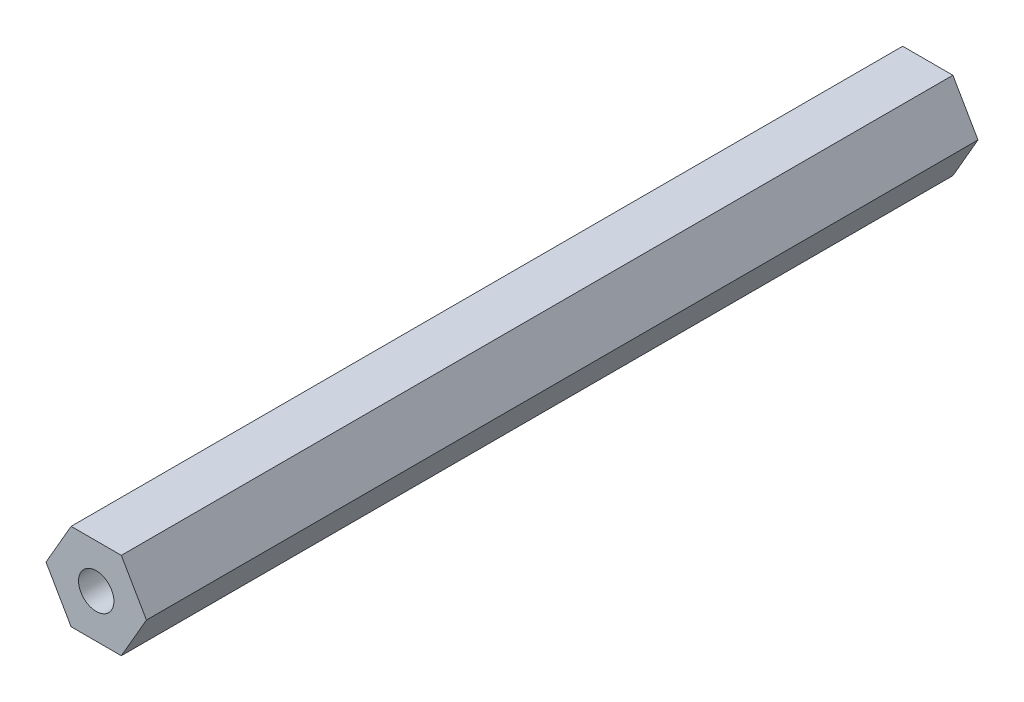
SolidWorks part; units mm, degrees
ref_plane "Front" through (0, 0, 0) normal (0, 0, 1) x (1, 0, 0)
ref_plane "Top" through (0, 0, 0) normal (0, 1, 0) x (1, 0, 0)
ref_plane "Right" through (0, 0, 0) normal (1, 0, 0) x (0, 0, -1)
sketch "Sketch1" plane through (0, 0, 0) normal (0, 0, 1) x (1, 0, 0)
  line L1 (7.3323, 0) -> (3.6662, 6.35)
  line L2 (3.6662, 6.35) -> (-3.6662, 6.35)
  line L3 (-3.6662, 6.35) -> (-7.3323, 0)
  line L4 (-7.3323, 0) -> (-3.6662, -6.35)
  line L5 (-3.6662, -6.35) -> (3.6662, -6.35)
  line L6 (3.6662, -6.35) -> (7.3323, 0)
  circle A0 centre (0, 0) radius 6.35 construction
extrude "Boss-Extrude1" add sketch "Sketch1" along normal blind 121.412
sketch "Sketch2" plane through (0, 0, 121.412) normal (0, 0, 1) x (1, 0, 0)
  circle A0 centre (0, 0) radius 2.5797
  dimension "D1" = 5.1594
extrude "Cut-Extrude1" cut sketch "Sketch2" against normal blind 12.7
ref_plane "Plane1" through (0, 0, 60.706) normal (0, 0, 1) x (1, 0, 0)
mirror "Mirror1" about plane through (0, 0, 60.706) normal (0, 0, 1) of "Cut-Extrude1"
